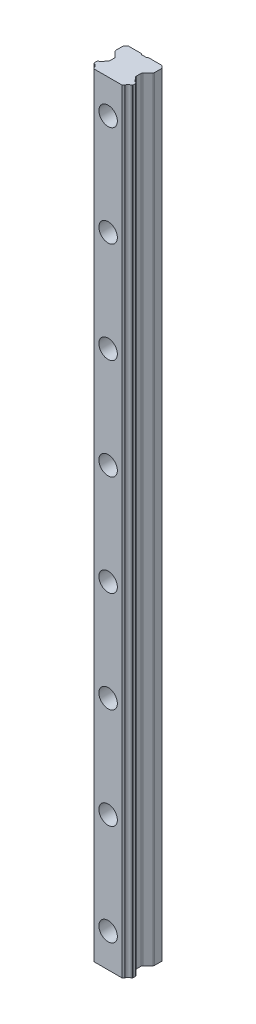
SolidWorks part; units mm, degrees
ref_plane "Płaszczyzna przednia" through (0, 0, 0) normal (0, 0, 1) x (1, 0, 0)
ref_plane "Płaszczyzna górna" through (0, 0, 0) normal (0, 1, 0) x (1, 0, 0)
ref_plane "Płaszczyzna prawa" through (0, 0, 0) normal (1, 0, 0) x (0, 0, -1)
ref_plane "Płaszczyzna1" through (0, 0, 0) normal (0, -1, 0) x (1, 0, 0)
sketch "Szkic1" plane through (0, 0, 0) normal (0, -1, 0) x (1, 0, 0)
  line L0 (-11.5, 6.2694) -> (-11.5, 0)
  line L1 (-11.5, 0) -> (11.5, 0)
  line L2 (11.5, 0) -> (11.5, 6.2694)
  line L3 (11.5, 6.2694) -> (7.9156, 9.8791)
  line L4 (7.9156, 9.8791) -> (7.9156, 13.5206)
  line L5 (7.9156, 13.5206) -> (8.9387, 14.5438)
  line L6 (11.0952, 16.6132) -> (11.5, 17.018)
  line L7 (11.5, 17.018) -> (11.5, 18.8316)
  line L8 (11.5, 18.8316) -> (11.0935, 19.2381)
  line L9 (9.0458, 21.2544) -> (8.3001, 22)
  line L10 (8.3001, 22) -> (-8.3001, 22)
  line L11 (-8.3001, 22) -> (-9.0458, 21.2544)
  line L12 (-11.0935, 19.2381) -> (-11.5, 18.8316)
  line L13 (-11.5, 18.8316) -> (-11.5, 17.018)
  line L14 (-11.5, 17.018) -> (-11.0952, 16.6132)
  line L15 (-8.9387, 14.5438) -> (-7.9156, 13.5206)
  line L16 (-7.9156, 13.5206) -> (-7.9156, 9.8791)
  line L17 (-7.9156, 9.8791) -> (-11.5, 6.2694)
  arc A0 (8.9387, 14.5438) -> (9.134, 14.763) centre (8.6794, 14.9712) ccw
  arc A1 (9.134, 14.763) -> (11.0952, 16.6132) centre (11.4771, 14.2438) cw
  arc A2 (11.0935, 19.2381) -> (9.1148, 21.1431) centre (11.4693, 21.6085) cw
  arc A3 (9.1148, 21.1431) -> (9.0458, 21.2544) centre (8.6749, 20.9471) ccw
  arc A4 (-9.0458, 21.2544) -> (-9.1148, 21.1431) centre (-8.6749, 20.9471) ccw
  arc A5 (-9.1148, 21.1431) -> (-11.0935, 19.2381) centre (-11.4693, 21.6085) cw
  arc A6 (-11.0952, 16.6132) -> (-9.134, 14.763) centre (-11.4771, 14.2438) cw
  arc A7 (-9.134, 14.763) -> (-8.9387, 14.5438) centre (-8.6794, 14.9712) ccw
extrude "Dodanie-wyciągnięcie1" add sketch "Szkic1" against normal blind 460
sketch "Szkic2" plane through (0, 460, 0) normal (0, 1, 0) x (-1, 0, 0)
  line L0 (-2.1067, 0) -> (2.1067, 0)
  line L1 (2.1067, 0) -> (1.5806, 0.5261)
  line L2 (1.5806, 0.5261) -> (-1.5806, 0.5261)
  line L3 (-1.5806, 0.5261) -> (-2.1067, 0)
extrude "Wytnij-wyciągnięcie1" cut sketch "Szkic2" against normal through all
ref_plane "Płaszczyzna2" through (0, 20, 0) normal (0, -1, 0) x (1, 0, 0)
sketch "Szkic7" plane through (0, 20, 0) normal (0, -1, 0) x (1, 0, 0)
  line L0 (5.5, 22) -> (0, 22)
  line L1 (0, 22) -> (0, 21.99)
  line L2 (0, 21.99) -> (5.5, 21.99)
  line L3 (5.5, 21.99) -> (5.5, 22)
  line L4 (0, 22) -> (0, 21.99) construction
revolve "Wycięcie-obrót1" cut sketch "Szkic7" angle 360 about L4
ref_plane "Płaszczyzna3" through (0, 80, 0) normal (0, -1, 0) x (1, 0, 0)
sketch "Szkic8" plane through (0, 80, 0) normal (0, -1, 0) x (1, 0, 0)
  line L0 (5.5, 22) -> (0, 22)
  line L1 (0, 22) -> (0, 21.99)
  line L2 (0, 21.99) -> (5.5, 21.99)
  line L3 (5.5, 21.99) -> (5.5, 22)
  line L4 (0, 22) -> (0, 21.99) construction
revolve "Wycięcie-obrót2" cut sketch "Szkic8" angle 360 about L4
ref_plane "Płaszczyzna4" through (0, 140, 0) normal (0, -1, 0) x (1, 0, 0)
sketch "Szkic9" plane through (0, 140, 0) normal (0, -1, 0) x (1, 0, 0)
  line L0 (5.5, 22) -> (0, 22)
  line L1 (0, 22) -> (0, 21.99)
  line L2 (0, 21.99) -> (5.5, 21.99)
  line L3 (5.5, 21.99) -> (5.5, 22)
  line L4 (0, 22) -> (0, 21.99) construction
revolve "Wycięcie-obrót3" cut sketch "Szkic9" angle 360 about L4
ref_plane "Płaszczyzna5" through (0, 200, 0) normal (0, -1, 0) x (1, 0, 0)
sketch "Szkic10" plane through (0, 200, 0) normal (0, -1, 0) x (1, 0, 0)
  line L0 (5.5, 22) -> (0, 22)
  line L1 (0, 22) -> (0, 21.99)
  line L2 (0, 21.99) -> (5.5, 21.99)
  line L3 (5.5, 21.99) -> (5.5, 22)
  line L4 (0, 22) -> (0, 21.99) construction
revolve "Wycięcie-obrót4" cut sketch "Szkic10" angle 360 about L4
ref_plane "Płaszczyzna6" through (0, 260, 0) normal (0, -1, 0) x (1, 0, 0)
sketch "Szkic11" plane through (0, 260, 0) normal (0, -1, 0) x (1, 0, 0)
  line L0 (5.5, 22) -> (0, 22)
  line L1 (0, 22) -> (0, 21.99)
  line L2 (0, 21.99) -> (5.5, 21.99)
  line L3 (5.5, 21.99) -> (5.5, 22)
  line L4 (0, 22) -> (0, 21.99) construction
revolve "Wycięcie-obrót5" cut sketch "Szkic11" angle 360 about L4
ref_plane "Płaszczyzna7" through (0, 320, 0) normal (0, -1, 0) x (1, 0, 0)
sketch "Szkic12" plane through (0, 320, 0) normal (0, -1, 0) x (1, 0, 0)
  line L0 (5.5, 22) -> (0, 22)
  line L1 (0, 22) -> (0, 21.99)
  line L2 (0, 21.99) -> (5.5, 21.99)
  line L3 (5.5, 21.99) -> (5.5, 22)
  line L4 (0, 22) -> (0, 21.99) construction
revolve "Wycięcie-obrót6" cut sketch "Szkic12" angle 360 about L4
ref_plane "Płaszczyzna8" through (0, 380, 0) normal (0, -1, 0) x (1, 0, 0)
sketch "Szkic13" plane through (0, 380, 0) normal (0, -1, 0) x (1, 0, 0)
  line L0 (5.5, 22) -> (0, 22)
  line L1 (0, 22) -> (0, 21.99)
  line L2 (0, 21.99) -> (5.5, 21.99)
  line L3 (5.5, 21.99) -> (5.5, 22)
  line L4 (0, 22) -> (0, 21.99) construction
revolve "Wycięcie-obrót7" cut sketch "Szkic13" angle 360 about L4
ref_plane "Płaszczyzna9" through (0, 440, 0) normal (0, -1, 0) x (1, 0, 0)
sketch "Szkic14" plane through (0, 440, 0) normal (0, -1, 0) x (1, 0, 0)
  line L0 (5.5, 22) -> (0, 22)
  line L1 (0, 22) -> (0, 21.99)
  line L2 (0, 21.99) -> (5.5, 21.99)
  line L3 (5.5, 21.99) -> (5.5, 22)
  line L4 (0, 22) -> (0, 21.99) construction
revolve "Wycięcie-obrót8" cut sketch "Szkic14" angle 360 about L4
ref_plane "Płaszczyzna10" [suppressed] through (0, 500, 0) normal (0, -1, 0) x (1, 0, 0)
sketch "Szkic15" [suppressed] plane through (0, 500, 0) normal (0, -1, 0) x (1, 0, 0)
  line L0 (5.5, 22) -> (0, 22)
  line L1 (0, 22) -> (0, 21.99)
  line L2 (0, 21.99) -> (5.5, 21.99)
  line L3 (5.5, 21.99) -> (5.5, 22)
  line L4 (0, 22) -> (0, 21.99) construction
revolve "Wycięcie-obrót9" [suppressed] cut sketch "Szkic15" angle 360 about L4
ref_plane "Płaszczyzna11" [suppressed] through (0, 560, 0) normal (0, -1, 0) x (1, 0, 0)
sketch "Szkic16" [suppressed] plane through (0, 560, 0) normal (0, -1, 0) x (1, 0, 0)
  line L0 (5.5, 22) -> (0, 22)
  line L1 (0, 22) -> (0, 21.99)
  line L2 (0, 21.99) -> (5.5, 21.99)
  line L3 (5.5, 21.99) -> (5.5, 22)
  line L4 (0, 22) -> (0, 21.99) construction
revolve "Wycięcie-obrót10" [suppressed] cut sketch "Szkic16" angle 360 about L4
ref_plane "Płaszczyzna12" [suppressed] through (0, 620, 0) normal (0, -1, 0) x (1, 0, 0)
sketch "Szkic17" [suppressed] plane through (0, 620, 0) normal (0, -1, 0) x (1, 0, 0)
  line L0 (5.5, 22) -> (0, 22)
  line L1 (0, 22) -> (0, 21.99)
  line L2 (0, 21.99) -> (5.5, 21.99)
  line L3 (5.5, 21.99) -> (5.5, 22)
  line L4 (0, 22) -> (0, 21.99) construction
revolve "Wycięcie-obrót11" [suppressed] cut sketch "Szkic17" angle 360 about L4
ref_plane "Płaszczyzna13" [suppressed] through (0, 680, 0) normal (0, -1, 0) x (1, 0, 0)
sketch "Szkic18" [suppressed] plane through (0, 680, 0) normal (0, -1, 0) x (1, 0, 0)
  line L0 (5.5, 22) -> (0, 22)
  line L1 (0, 22) -> (0, 21.99)
  line L2 (0, 21.99) -> (5.5, 21.99)
  line L3 (5.5, 21.99) -> (5.5, 22)
  line L4 (0, 22) -> (0, 21.99) construction
revolve "Wycięcie-obrót12" [suppressed] cut sketch "Szkic18" angle 360 about L4
ref_plane "Płaszczyzna14" [suppressed] through (0, 740, 0) normal (0, -1, 0) x (1, 0, 0)
sketch "Szkic19" [suppressed] plane through (0, 740, 0) normal (0, -1, 0) x (1, 0, 0)
  line L0 (5.5, 22) -> (0, 22)
  line L1 (0, 22) -> (0, 21.99)
  line L2 (0, 21.99) -> (5.5, 21.99)
  line L3 (5.5, 21.99) -> (5.5, 22)
  line L4 (0, 22) -> (0, 21.99) construction
revolve "Wycięcie-obrót13" [suppressed] cut sketch "Szkic19" angle 360 about L4
ref_plane "Płaszczyzna15" [suppressed] through (0, 800, 0) normal (0, -1, 0) x (1, 0, 0)
sketch "Szkic20" [suppressed] plane through (0, 800, 0) normal (0, -1, 0) x (1, 0, 0)
  line L0 (5.5, 22) -> (0, 22)
  line L1 (0, 22) -> (0, 21.99)
  line L2 (0, 21.99) -> (5.5, 21.99)
  line L3 (5.5, 21.99) -> (5.5, 22)
  line L4 (0, 22) -> (0, 21.99) construction
revolve "Wycięcie-obrót14" [suppressed] cut sketch "Szkic20" angle 360 about L4
ref_plane "Płaszczyzna16" [suppressed] through (0, 860, 0) normal (0, -1, 0) x (1, 0, 0)
sketch "Szkic21" [suppressed] plane through (0, 860, 0) normal (0, -1, 0) x (1, 0, 0)
  line L0 (5.5, 22) -> (0, 22)
  line L1 (0, 22) -> (0, 21.99)
  line L2 (0, 21.99) -> (5.5, 21.99)
  line L3 (5.5, 21.99) -> (5.5, 22)
  line L4 (0, 22) -> (0, 21.99) construction
revolve "Wycięcie-obrót15" [suppressed] cut sketch "Szkic21" angle 360 about L4
ref_plane "Płaszczyzna17" [suppressed] through (0, 920, 0) normal (0, -1, 0) x (1, 0, 0)
sketch "Szkic22" [suppressed] plane through (0, 920, 0) normal (0, -1, 0) x (1, 0, 0)
  line L0 (5.5, 22) -> (0, 22)
  line L1 (0, 22) -> (0, 21.99)
  line L2 (0, 21.99) -> (5.5, 21.99)
  line L3 (5.5, 21.99) -> (5.5, 22)
  line L4 (0, 22) -> (0, 21.99) construction
revolve "Wycięcie-obrót16" [suppressed] cut sketch "Szkic22" angle 360 about L4
ref_plane "Płaszczyzna18" [suppressed] through (0, 980, 0) normal (0, -1, 0) x (1, 0, 0)
sketch "Szkic23" [suppressed] plane through (0, 980, 0) normal (0, -1, 0) x (1, 0, 0)
  line L0 (5.5, 22) -> (0, 22)
  line L1 (0, 22) -> (0, 21.99)
  line L2 (0, 21.99) -> (5.5, 21.99)
  line L3 (5.5, 21.99) -> (5.5, 22)
  line L4 (0, 22) -> (0, 21.99) construction
revolve "Wycięcie-obrót17" [suppressed] cut sketch "Szkic23" angle 360 about L4
sketch "Szkic24" plane through (0, 20, 0) normal (0, -1, 0) x (1, 0, 0)
  line L0 (5.5, 22) -> (0, 22)
  line L1 (0, 22) -> (0, 0)
  line L2 (0, 0) -> (3.5, 0)
  line L3 (3.5, 0) -> (3.5, 13)
  line L4 (3.5, 13) -> (5.5, 13)
  line L5 (5.5, 13) -> (5.5, 22)
  line L6 (0, 22) -> (0, 0) construction
  dimension "D1" = 22
revolve "Wycięcie-obrót18" cut sketch "Szkic24" angle 360 about L6
sketch "Szkic25" plane through (0, 80, 0) normal (0, -1, 0) x (1, 0, 0)
  line L0 (5.5, 22) -> (0, 22)
  line L1 (0, 22) -> (0, 0)
  line L2 (0, 0) -> (3.5, 0)
  line L3 (3.5, 0) -> (3.5, 13)
  line L4 (3.5, 13) -> (5.5, 13)
  line L5 (5.5, 13) -> (5.5, 22)
  line L6 (0, 22) -> (0, 0) construction
  dimension "D1" = 22
revolve "Wycięcie-obrót19" cut sketch "Szkic25" angle 360 about L6
sketch "Szkic26" plane through (0, 140, 0) normal (0, -1, 0) x (1, 0, 0)
  line L0 (5.5, 22) -> (0, 22)
  line L1 (0, 22) -> (0, 0)
  line L2 (0, 0) -> (3.5, 0)
  line L3 (3.5, 0) -> (3.5, 13)
  line L4 (3.5, 13) -> (5.5, 13)
  line L5 (5.5, 13) -> (5.5, 22)
  line L6 (0, 22) -> (0, 0) construction
  dimension "D1" = 22
revolve "Wycięcie-obrót20" cut sketch "Szkic26" angle 360 about L6
sketch "Szkic27" plane through (0, 200, 0) normal (0, -1, 0) x (1, 0, 0)
  line L0 (5.5, 22) -> (0, 22)
  line L1 (0, 22) -> (0, 0)
  line L2 (0, 0) -> (3.5, 0)
  line L3 (3.5, 0) -> (3.5, 13)
  line L4 (3.5, 13) -> (5.5, 13)
  line L5 (5.5, 13) -> (5.5, 22)
  line L6 (0, 22) -> (0, 0) construction
  dimension "D1" = 22
revolve "Wycięcie-obrót21" cut sketch "Szkic27" angle 360 about L6
sketch "Szkic28" plane through (0, 260, 0) normal (0, -1, 0) x (1, 0, 0)
  line L0 (5.5, 22) -> (0, 22)
  line L1 (0, 22) -> (0, 0)
  line L2 (0, 0) -> (3.5, 0)
  line L3 (3.5, 0) -> (3.5, 13)
  line L4 (3.5, 13) -> (5.5, 13)
  line L5 (5.5, 13) -> (5.5, 22)
  line L6 (0, 22) -> (0, 0) construction
  dimension "D1" = 22
revolve "Wycięcie-obrót22" cut sketch "Szkic28" angle 360 about L6
sketch "Szkic29" plane through (0, 320, 0) normal (0, -1, 0) x (1, 0, 0)
  line L0 (5.5, 22) -> (0, 22)
  line L1 (0, 22) -> (0, 0)
  line L2 (0, 0) -> (3.5, 0)
  line L3 (3.5, 0) -> (3.5, 13)
  line L4 (3.5, 13) -> (5.5, 13)
  line L5 (5.5, 13) -> (5.5, 22)
  line L6 (0, 22) -> (0, 0) construction
  dimension "D1" = 22
revolve "Wycięcie-obrót23" cut sketch "Szkic29" angle 360 about L6
sketch "Szkic30" plane through (0, 380, 0) normal (0, -1, 0) x (1, 0, 0)
  line L0 (5.5, 22) -> (0, 22)
  line L1 (0, 22) -> (0, 0)
  line L2 (0, 0) -> (3.5, 0)
  line L3 (3.5, 0) -> (3.5, 13)
  line L4 (3.5, 13) -> (5.5, 13)
  line L5 (5.5, 13) -> (5.5, 22)
  line L6 (0, 22) -> (0, 0) construction
  dimension "D1" = 22
revolve "Wycięcie-obrót24" cut sketch "Szkic30" angle 360 about L6
sketch "Szkic31" plane through (0, 440, 0) normal (0, -1, 0) x (1, 0, 0)
  line L0 (5.5, 22) -> (0, 22)
  line L1 (0, 22) -> (0, 0)
  line L2 (0, 0) -> (3.5, 0)
  line L3 (3.5, 0) -> (3.5, 13)
  line L4 (3.5, 13) -> (5.5, 13)
  line L5 (5.5, 13) -> (5.5, 22)
  line L6 (0, 22) -> (0, 0) construction
  dimension "D1" = 22
revolve "Wycięcie-obrót25" cut sketch "Szkic31" angle 360 about L6
sketch "Szkic32" [suppressed] plane through (0, 500, 0) normal (0, -1, 0) x (1, 0, 0)
  line L0 (5.5, 22) -> (0, 22)
  line L1 (0, 22) -> (0, 0)
  line L2 (0, 0) -> (3.5, 0)
  line L3 (3.5, 0) -> (3.5, 13)
  line L4 (3.5, 13) -> (5.5, 13)
  line L5 (5.5, 13) -> (5.5, 22)
  line L6 (0, 22) -> (0, 0) construction
  dimension "D1" = 22
revolve "Wycięcie-obrót26" [suppressed] cut sketch "Szkic32" angle 360 about L6
sketch "Szkic33" [suppressed] plane through (0, 560, 0) normal (0, -1, 0) x (1, 0, 0)
  line L0 (5.5, 22) -> (0, 22)
  line L1 (0, 22) -> (0, 0)
  line L2 (0, 0) -> (3.5, 0)
  line L3 (3.5, 0) -> (3.5, 13)
  line L4 (3.5, 13) -> (5.5, 13)
  line L5 (5.5, 13) -> (5.5, 22)
  line L6 (0, 22) -> (0, 0) construction
  dimension "D1" = 22
revolve "Wycięcie-obrót27" [suppressed] cut sketch "Szkic33" angle 360 about L6
sketch "Szkic34" [suppressed] plane through (0, 620, 0) normal (0, -1, 0) x (1, 0, 0)
  line L0 (5.5, 22) -> (0, 22)
  line L1 (0, 22) -> (0, 0)
  line L2 (0, 0) -> (3.5, 0)
  line L3 (3.5, 0) -> (3.5, 13)
  line L4 (3.5, 13) -> (5.5, 13)
  line L5 (5.5, 13) -> (5.5, 22)
  line L6 (0, 22) -> (0, 0) construction
  dimension "D1" = 22
revolve "Wycięcie-obrót28" [suppressed] cut sketch "Szkic34" angle 360 about L6
sketch "Szkic35" [suppressed] plane through (0, 680, 0) normal (0, -1, 0) x (1, 0, 0)
  line L0 (5.5, 22) -> (0, 22)
  line L1 (0, 22) -> (0, 0)
  line L2 (0, 0) -> (3.5, 0)
  line L3 (3.5, 0) -> (3.5, 13)
  line L4 (3.5, 13) -> (5.5, 13)
  line L5 (5.5, 13) -> (5.5, 22)
  line L6 (0, 22) -> (0, 0) construction
  dimension "D1" = 22
revolve "Wycięcie-obrót29" [suppressed] cut sketch "Szkic35" angle 360 about L6
sketch "Szkic36" [suppressed] plane through (0, 740, 0) normal (0, -1, 0) x (1, 0, 0)
  line L0 (5.5, 22) -> (0, 22)
  line L1 (0, 22) -> (0, 0)
  line L2 (0, 0) -> (3.5, 0)
  line L3 (3.5, 0) -> (3.5, 13)
  line L4 (3.5, 13) -> (5.5, 13)
  line L5 (5.5, 13) -> (5.5, 22)
  line L6 (0, 22) -> (0, 0) construction
  dimension "D1" = 22
revolve "Wycięcie-obrót30" [suppressed] cut sketch "Szkic36" angle 360 about L6
sketch "Szkic37" [suppressed] plane through (0, 800, 0) normal (0, -1, 0) x (1, 0, 0)
  line L0 (5.5, 22) -> (0, 22)
  line L1 (0, 22) -> (0, 0)
  line L2 (0, 0) -> (3.5, 0)
  line L3 (3.5, 0) -> (3.5, 13)
  line L4 (3.5, 13) -> (5.5, 13)
  line L5 (5.5, 13) -> (5.5, 22)
  line L6 (0, 22) -> (0, 0) construction
  dimension "D1" = 22
revolve "Wycięcie-obrót31" [suppressed] cut sketch "Szkic37" angle 360 about L6
sketch "Szkic38" [suppressed] plane through (0, 860, 0) normal (0, -1, 0) x (1, 0, 0)
  line L0 (5.5, 22) -> (0, 22)
  line L1 (0, 22) -> (0, 0)
  line L2 (0, 0) -> (3.5, 0)
  line L3 (3.5, 0) -> (3.5, 13)
  line L4 (3.5, 13) -> (5.5, 13)
  line L5 (5.5, 13) -> (5.5, 22)
  line L6 (0, 22) -> (0, 0) construction
  dimension "D1" = 22
revolve "Wycięcie-obrót32" [suppressed] cut sketch "Szkic38" angle 360 about L6
sketch "Szkic39" [suppressed] plane through (0, 920, 0) normal (0, -1, 0) x (1, 0, 0)
  line L0 (5.5, 22) -> (0, 22)
  line L1 (0, 22) -> (0, 0)
  line L2 (0, 0) -> (3.5, 0)
  line L3 (3.5, 0) -> (3.5, 13)
  line L4 (3.5, 13) -> (5.5, 13)
  line L5 (5.5, 13) -> (5.5, 22)
  line L6 (0, 22) -> (0, 0) construction
  dimension "D1" = 22
revolve "Wycięcie-obrót33" [suppressed] cut sketch "Szkic39" angle 360 about L6
sketch "Szkic40" [suppressed] plane through (0, 980, 0) normal (0, -1, 0) x (1, 0, 0)
  line L0 (5.5, 22) -> (0, 22)
  line L1 (0, 22) -> (0, 0)
  line L2 (0, 0) -> (3.5, 0)
  line L3 (3.5, 0) -> (3.5, 13)
  line L4 (3.5, 13) -> (5.5, 13)
  line L5 (5.5, 13) -> (5.5, 22)
  line L6 (0, 22) -> (0, 0) construction
  dimension "D1" = 22
revolve "Wycięcie-obrót34" [suppressed] cut sketch "Szkic40" angle 360 about L6
chamfer "Sfazowanie2" distance 1.5279 angle 44.867 1 edges at (11.5, 230, 0)
chamfer "Sfazowanie4" distance 1.5208 angle 45.133 1 edges at (-11.5, 230, 0)
fillet "Zaokrąglenie1" radius 0.5 8 edges at (-11.0952, 230, 16.6132) (-11.5, 230, 17.018) (11.0935, 230, 19.2381) (11.5, 230, 18.8316) (-11.0935, 230, 19.2381) (-11.5, 230, 18.8316) (11.5, 230, 17.018) (11.0952, 230, 16.6132)
fillet "Zaokrąglenie2" radius 1 6 edges at (-7.9156, 230, 13.5206) (-11.5, 230, 6.2694) (-7.9156, 230, 9.8791) (7.9156, 230, 9.8791) (7.9156, 230, 13.5206) (11.5, 230, 6.2694)
